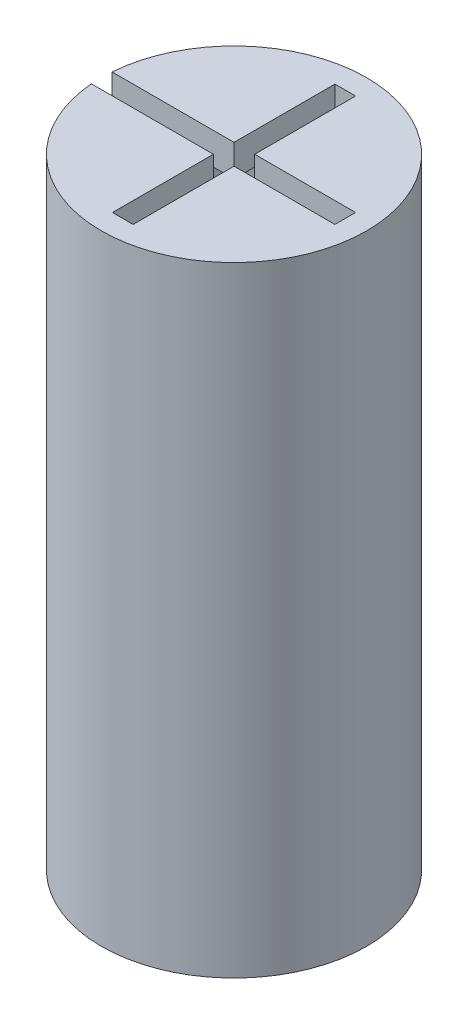
SolidWorks part; units mm, degrees
ref_plane "Front Plane" through (0, 0, 0) normal (0, 0, 1) x (1, 0, 0)
ref_plane "Top Plane" through (0, 0, 0) normal (0, 1, 0) x (1, 0, 0)
ref_plane "Right Plane" through (0, 0, 0) normal (1, 0, 0) x (0, 0, -1)
sketch "Sketch1" plane through (0, 0, 0) normal (0, 0, 1) x (1, 0, 0)
  line L0 (0, 0) -> (0, 39) construction
  line L1 (-6.35, 0) -> (-8.35, 0)
  line L2 (-8.35, 0) -> (-8.35, 39)
  line L3 (-8.35, 39) -> (0, 39)
  line L4 (-4.35, 37) -> (-4.35, 21)
  line L5 (-4.35, 21) -> (-6.35, 21)
  line L6 (-6.35, 21) -> (-6.35, 0)
  line L7 (-4.35, 37) -> (0, 37)
  line L8 (0, 37) -> (0, 39)
  point P1 (0, 0)
  point P12 (0, 0)
  dimension "D1" = 2
  dimension "D2" = 21
  dimension "D3" = 37
  dimension "D4" = 12.7
revolve "Revolve1" add sketch "Sketch1" angle 360 about L0
sketch "Sketch2" plane through (0, 39, 0) normal (0, 1, 0) x (1, 0, 0)
  line L5 (-0.65, 0.65) -> (-7, 0.65)
  line L6 (7, -0.65) -> (0.65, -0.65)
  line L7 (7, -0.65) -> (7, 0.65)
  line L8 (0.65, -7) -> (-0.65, -7)
  line L9 (0.65, -7) -> (0.65, -0.65)
  line L10 (0.65, 7) -> (-0.65, 7)
  line L11 (-0.65, -7) -> (-0.65, -0.65)
  line L12 (0.65, -7) -> (-0.65, 7) construction
  line L13 (0.65, 7) -> (-0.65, -7) construction
  line L14 (7, 0.65) -> (0.65, 0.65)
  line L16 (7, -0.65) -> (-7, 0.65) construction
  line L17 (7, 0.65) -> (-7, -0.65) construction
  line L18 (-7, 0.65) -> (-11.6622, 0.65)
  line L20 (-7, -0.65) -> (-11.6622, -0.65)
  line L21 (-11.6622, 0.65) -> (-11.6622, -0.65)
  line L22 (-0.65, 0.65) -> (-0.65, 7)
  line L23 (0.65, 0.65) -> (0.65, 7)
  line L27 (-0.65, -0.65) -> (-7, -0.65)
  point P0 (0, 0)
  dimension "D1" = 1.3
extrude "Cut-Extrude1" cut sketch "Sketch2" against normal through all both and the other way through all
